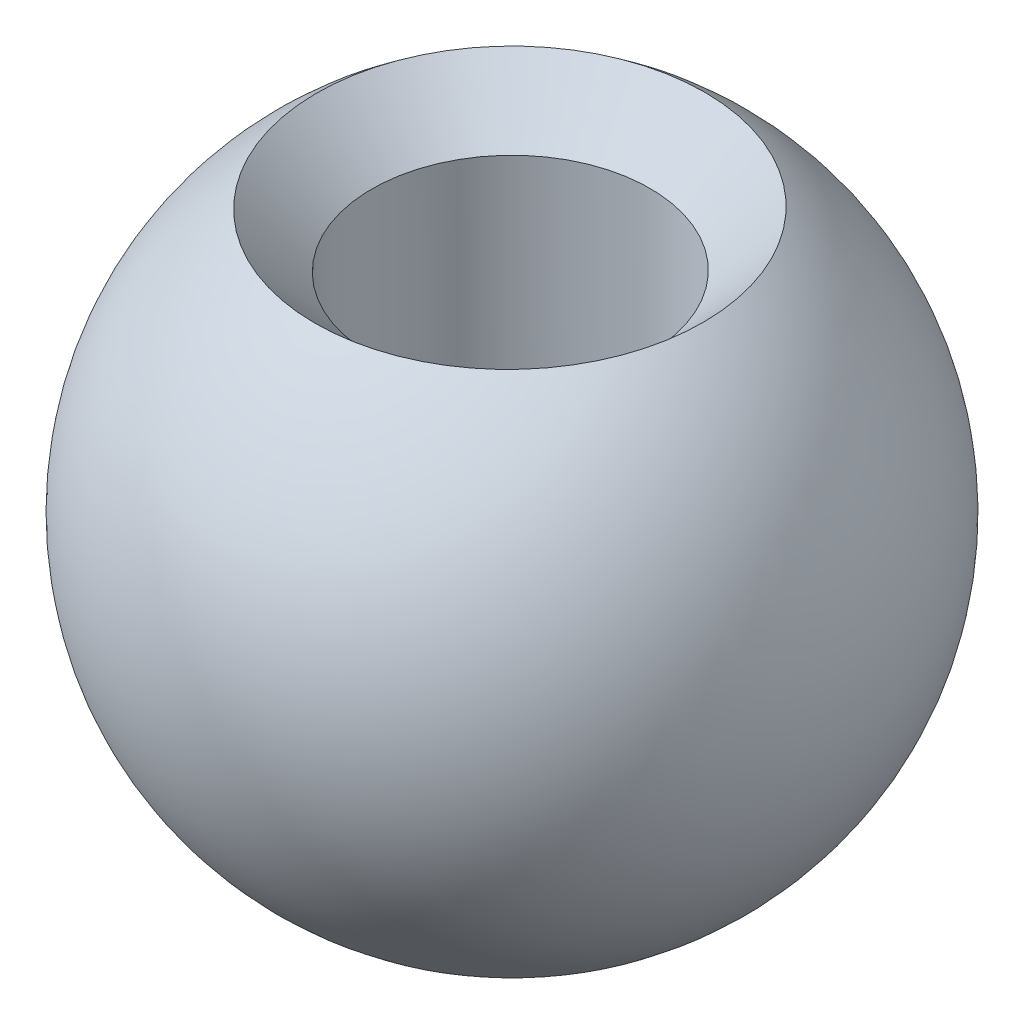
SolidWorks part; units mm, degrees
ref_plane "Спереди" through (0, 0, 0) normal (0, 0, 1) x (1, 0, 0)
ref_plane "Сверху" through (0, 0, 0) normal (0, 1, 0) x (1, 0, 0)
ref_plane "Справа" through (0, 0, 0) normal (1, 0, 0) x (0, 0, -1)
sketch "Эскиз1" plane through (0, 0, 0) normal (0, 1, 0) x (1, 0, 0)
  line L0 (4, 0) -> (-4, 0)
  arc A0 (-4, 0) -> (4, 0) centre (0, 0) cw
  point P4 (0, 0)
  dimension "D1" = 8
revolve "Повернуть1" add sketch "Эскиз1" angle 360 about L0
sketch3d "Трехмерный эскиз7"
  point P0 (0.0512, 3.9674, -0.5069)
ref_plane "Плоскость3" through (0, 3.3674, 0) normal (0, 1, 0) x (1, 0, 0)
hole_wizard "Зенковка для  винта с плоской головкой M32" positions "Трехмерный эскиз9" profile "Эскиз7" countersink size "M3" standard "Ansi Metric" end condition through all
sketch3d "Трехмерный эскиз9"
  point P0 (0.0116, 3.9997, 0.0438)
sketch "Эскиз7" plane through (0.0116, 3.9997, 0.0438) normal (0.7071, -0.0098, 0.7071) x (-0.7071, -0.0057, 0.7071)
  line L0 (0, 0) -> (0, 8.0551)
  line L1 (0, 8.0551) -> (1.7, 8.0551)
  line L2 (1.7, 8.0551) -> (1.7, 1.45)
  line L3 (1.7, 1.45) -> (3.15, 0)
  line L5 (3.15, 0) -> (0, 0)
  line L6 (-1.7, 1.45) -> (-3.15, 0) construction
  line L11 (0, -6.35) -> (0, 107.95) construction
  dimension "Диаметр сквозного отверстия" = 3.4
  dimension "Глубина сквозного отверстия" = 8.0551
  dimension "Диаметр передней зенковки" = 6.3
  dimension "Угол передней зенковки" = 90
